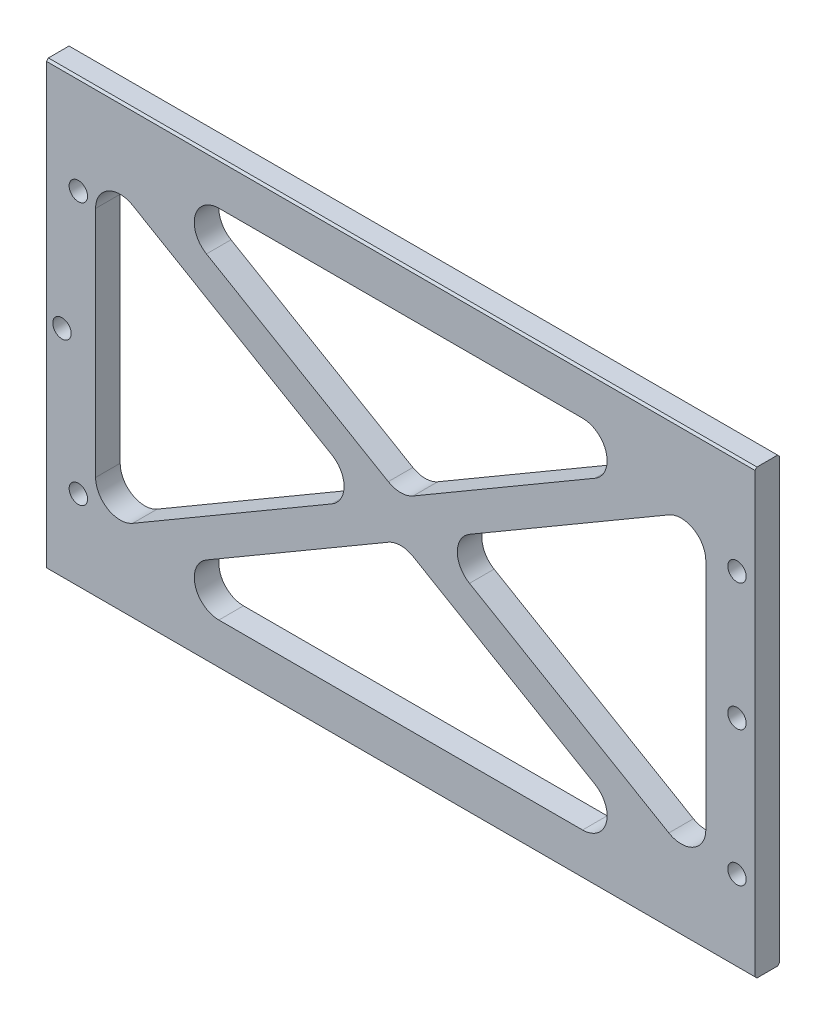
SolidWorks part; units mm, degrees
material "6061-T6 Al"
ref_plane "Front" through (0, 0, 0) normal (0, 0, 1) x (1, 0, 0)
ref_plane "Top" through (0, 0, 0) normal (0, 1, 0) x (1, 0, 0)
ref_plane "Right" through (0, 0, 0) normal (1, 0, 0) x (0, 0, -1)
sketch "Sketch1" plane through (0, 0, 0) normal (0, 0, 1) x (1, 0, 0)
  line L1 (0, 0) -> (274.5232, 0)
  line L2 (0, 0) -> (0, 171.45)
  line L3 (0, 171.45) -> (274.5232, 171.45)
  line L4 (274.5232, 0) -> (274.5232, 171.45)
  dimension "D1" = 274.5232
  dimension "D2" = 171.45
extrude "Boss-Extrude1" add sketch "Sketch1" along normal blind 9.525
hole_wizard "9/32 (0.28125) Diameter Hole1" positions "Sketch4" profile "Sketch5" hole size "9/32" standard "Ansi Inch" end condition through all
sketch "Sketch4" plane through (0, 0, 9.525) normal (0, 0, 1) x (1, 0, 0)
  line L2 (267.5382, 133.35) -> (267.5382, 84.1248) construction
  line L3 (267.5382, 84.1248) -> (267.5382, 31.75) construction
  line L4 (12.3698, 133.35) -> (267.5382, 133.35) construction
  line L5 (6.0198, 84.1248) -> (267.5382, 84.1248) construction
  line L6 (12.3698, 31.75) -> (267.5382, 31.75) construction
  line L7 (0, 171.45) -> (0, 0) construction
  line L8 (274.5232, 171.45) -> (0, 171.45) construction
  line L9 (12.3698, 133.35) -> (12.3698, 31.75) construction
  line L10 (274.5232, 0) -> (274.5232, 171.45) construction
  point P0 (6.0198, 84.1248)
  point P1 (12.3698, 133.35)
  point P6 (12.3698, 31.75)
  point P9 (267.5382, 133.35)
  point P12 (267.5382, 84.1248)
  point P15 (267.5382, 31.75)
  dimension "D1" = 0
  dimension "D2" = 6.0198
  dimension "D3" = 6.985
  dimension "D4" = 0
  dimension "D5" = 38.1
  dimension "D6" = 49.2252
  dimension "D7" = 52.3748
  dimension "D8" = 6.35
sketch "Sketch5" plane through (6.0198, 84.1248, 9.525) normal (1, 0, 0) x (0, -1, 0)
  line L0 (0, 0) -> (0, 9.525)
  line L1 (0, 9.525) -> (3.5719, 9.525)
  line L2 (3.5719, 9.525) -> (3.5719, 0)
  line L5 (3.5719, 0) -> (0, 0)
  line L11 (0, -6.35) -> (0, 107.95) construction
  dimension "Thru Hole Dia." = 7.1437
  dimension "Thru Hole Depth" = 9.525
chamfer "Chamfer1" distance 0.762 angle 45 4 edges at (137.2616, 0, 0) (137.2616, 0, 9.525) (137.2616, 171.45, 0) (137.2616, 171.45, 9.525)
sketch "Sketch6" plane through (0, 0, 9.525) normal (0, 0, 1) x (1, 0, 0)
  line L0 (0, 85.725) -> (19.05, 85.725) construction
  line L1 (19.05, 154.813) -> (255.4732, 154.813) construction
  line L2 (19.05, 154.813) -> (19.05, 16.637) construction
  line L3 (19.05, 16.637) -> (255.4732, 16.637) construction
  line L5 (255.4732, 154.813) -> (255.4732, 16.637) construction
  line L6 (0, 170.688) -> (0, 0.762) construction
  line L7 (137.2616, 170.688) -> (137.2616, 154.813) construction
  line L8 (274.5232, 170.688) -> (0, 170.688) construction
  line L11 (274.5232, 0.762) -> (274.5232, 170.688) construction
  line L12 (19.05, 154.813) -> (255.4732, 16.637) construction
  line L14 (255.4732, 154.813) -> (19.05, 16.637) construction
  line L15 (33.3812, 139.0823) -> (110.6063, 93.9485)
  line L20 (62.0028, 137.0645) -> (132.4554, 95.8889)
  line L21 (212.5204, 137.0645) -> (142.0678, 95.8889)
  line L22 (241.142, 139.0823) -> (163.9169, 93.9485)
  line L23 (66.809, 154.813) -> (207.7142, 154.813)
  line L24 (19.05, 130.8587) -> (19.05, 40.5913)
  line L25 (66.809, 16.637) -> (207.7142, 16.637)
  line L26 (255.4732, 130.8587) -> (255.4732, 40.5913)
  line L27 (110.6063, 77.5015) -> (33.3812, 32.3677)
  line L28 (22.2541, 160.2953) -> (258.6773, 22.1193) construction
  line L29 (252.2691, 160.2953) -> (15.8459, 22.1193) construction
  line L30 (258.6773, 149.3307) -> (22.2541, 11.1547) construction
  line L31 (15.8459, 149.3307) -> (252.2691, 11.1547) construction
  line L32 (132.4554, 75.5611) -> (62.0028, 34.3855)
  line L33 (163.9169, 77.5015) -> (241.142, 32.3677)
  line L34 (142.0678, 75.5611) -> (212.5204, 34.3855)
  arc A0 (132.4554, 95.8889) -> (142.0678, 95.8889) centre (137.2616, 104.1124) ccw
  arc A1 (62.0028, 137.0645) -> (66.809, 154.813) centre (66.809, 145.288) cw
  arc A2 (207.7142, 154.813) -> (212.5204, 137.0645) centre (207.7142, 145.288) cw
  arc A3 (241.142, 32.3677) -> (255.4732, 40.5913) centre (245.9482, 40.5913) ccw
  arc A4 (241.142, 139.0823) -> (255.4732, 130.8587) centre (245.9482, 130.8587) cw
  arc A5 (163.9169, 93.9485) -> (163.9169, 77.5015) centre (168.723, 85.725) ccw
  arc A6 (62.0028, 34.3855) -> (66.809, 16.637) centre (66.809, 26.162) ccw
  arc A7 (207.7142, 16.637) -> (212.5204, 34.3855) centre (207.7142, 26.162) ccw
  arc A8 (142.0678, 75.5611) -> (132.4554, 75.5611) centre (137.2616, 67.3376) ccw
  arc A9 (110.6063, 93.9485) -> (110.6063, 77.5015) centre (105.8002, 85.725) cw
  arc A10 (19.05, 40.5913) -> (33.3812, 32.3677) centre (28.575, 40.5913) ccw
  arc A11 (19.05, 130.8587) -> (33.3812, 139.0823) centre (28.575, 130.8587) cw
  point P38 (31.6346, 154.813)
  point P41 (242.8886, 154.813)
  point P44 (255.4732, 23.992)
  point P47 (255.4732, 147.458)
  point P50 (149.8462, 85.725)
  point P53 (31.6346, 16.637)
  point P56 (242.8886, 16.637)
  point P59 (137.2616, 78.37)
  point P64 (19.05, 23.992)
  point P67 (19.05, 147.458)
  dimension "D7" = 9.525
  dimension "D1" = 15.875
  dimension "D2" = 19.05
  dimension "web width" = 6.35
extrude "Cut-Extrude1" cut sketch "Sketch6" against normal through all
